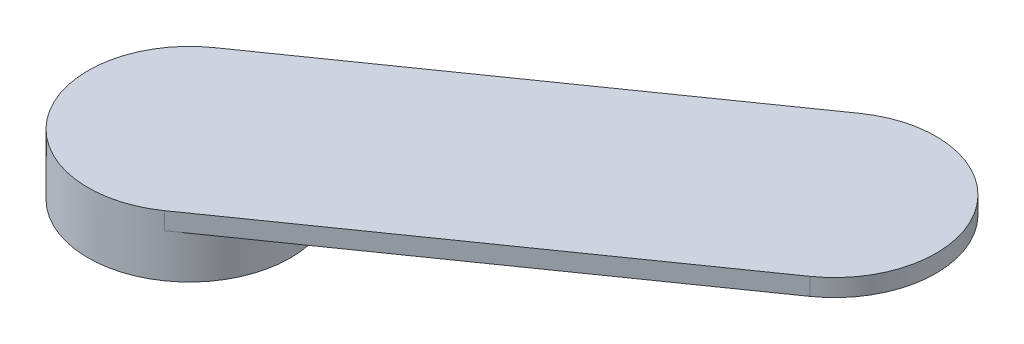
SolidWorks part; units mm, degrees
ref_plane "Front Plane" through (0, 0, 0) normal (0, 0, 1) x (1, 0, 0)
ref_plane "Top Plane" through (0, 0, 0) normal (0, 1, 0) x (1, 0, 0)
ref_plane "Right Plane" through (0, 0, 0) normal (1, 0, 0) x (0, 0, -1)
sketch "Sketch1" plane through (0, 0, 0) normal (0, 1, 0) x (1, 0, 0)
  line L0 (0, 0) -> (131.0643, 91.7722) construction
  line L1 (-20.0752, 28.6703) -> (110.9892, 120.4426)
  line L2 (20.0752, -28.6703) -> (151.1395, 63.1019)
  line L3 (0, 0) -> (251.7317, 0) construction
  arc A0 (-20.0752, 28.6703) -> (20.0752, -28.6703) centre (0, 0) ccw
  arc A1 (151.1395, 63.1019) -> (110.9892, 120.4426) centre (131.0643, 91.7722) ccw
  point P3 (65.5322, 45.8861)
  dimension "D1" = 35
  dimension "D2" = 160
  dimension "D3" = 35
extrude "Boss-Extrude1" add sketch "Sketch1" against normal blind 6 contours L2 A1 L1 A0
sketch "Sketch2" plane through (0, -6, 0) normal (0, -1, 0) x (1, 0, 0)
  circle A0 centre (0, 0) radius 35
extrude "Boss-Extrude2" add sketch "Sketch2" along normal blind 15
